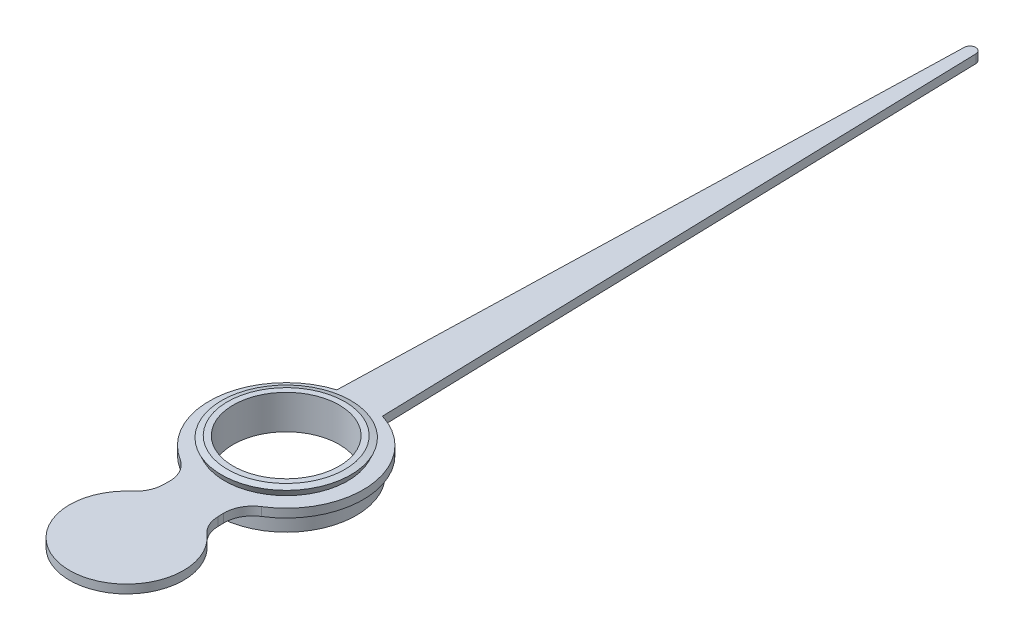
SolidWorks part; units mm, degrees
ref_plane "Face" through (0, 0, 0) normal (0, 0, 1) x (1, 0, 0)
ref_plane "Dessus" through (0, 0, 0) normal (0, 1, 0) x (1, 0, 0)
ref_plane "Droite" through (0, 0, 0) normal (1, 0, 0) x (0, 0, -1)
sketch "Esquisse1" plane through (0, 0, 0) normal (0, 0, 1) x (1, 0, 0)
  line L0 (-1.23, 0) -> (-1.23, 0.3)
  line L1 (-1.23, 0.3) -> (-1.08, 0.3)
  line L2 (-1.08, 0.3) -> (-1.08, 0.45)
  line L3 (-1.0301, 0.6) -> (-0.93, 0.6)
  line L4 (-0.93, 0.6) -> (-0.93, 0)
  line L5 (-0.93, 0) -> (-1.23, 0)
  line L6 (-0.93, 0) -> (0, 0) construction
  line L7 (0, 0) -> (0, 7.0792) construction
  line L8 (-1.08, 0.45) -> (-1.1325, 0.5676)
  line L9 (-1.1325, 0.5676) -> (-1.0301, 0.6)
  dimension "D1" = 1.86
  dimension "D2" = 0.3
  dimension "D3" = 0.3
  dimension "D4" = 0.15
  dimension "D5" = 0.6
  dimension "D6" = 0.0525
  dimension "D7" = 0.1001
  dimension "D8" = 0.15
  dimension "D9" = 0.1176
revolve "Révolution1" add sketch "Esquisse1" angle 360 about L7
sketch "Esquisse2" plane through (0, 0.3, 0) normal (0, 1, 0) x (1, 0, 0)
  line L0 (0.1, 12.0028) -> (0.4, 1.2894)
  line L1 (-0.4804, -1.583) -> (-0.4832, -1.6829)
  line L2 (0, -6.2879) -> (0, -1.265) construction
  line L4 (0.4832, -1.6829) -> (0.4804, -1.583)
  line L5 (0.4, 1.2894) -> (0, 1.2894) construction
  line L6 (0, 1.2894) -> (-0.4, 1.2894) construction
  line L7 (0, 16) -> (0, 1.2894) construction
  line L8 (-0.4, 1.2894) -> (-0.1, 12.0028)
  line L9 (-0.4715, -1.265) -> (0.4715, -1.265) construction
  line L10 (0, -1.08) -> (0, 0) construction
  arc A0 (-0.4, 1.2894) -> (-0.7153, -1.1449) centre (0, 0) ccw
  circle A1 centre (0, 0) radius 1.08
  circle A2 centre (0, 0) radius 1.08 construction
  arc A3 (0.7153, -1.1449) -> (0.4, 1.2894) centre (0, 0) ccw
  arc A4 (-0.6554, -2.0466) -> (0.6554, -2.0466) centre (0, -2.8019) ccw
  arc A5 (0.7153, -1.1449) -> (0.4804, -1.583) centre (0.9802, -1.569) ccw
  arc A6 (0.6554, -2.0466) -> (0.4832, -1.6829) centre (0.983, -1.6689) cw
  arc A7 (-0.6554, -2.0466) -> (-0.4832, -1.6829) centre (-0.983, -1.6689) ccw
  arc A8 (-0.1, 12.0028) -> (0.1, 12.0028) centre (0, 12) cw
  arc A9 (-0.4804, -1.583) -> (-0.7153, -1.1449) centre (-0.9802, -1.569) ccw
  point P26 (0, -3.144)
  dimension "D1" = 2.7
  dimension "D5" = 0.1
  dimension "D6" = 1
  dimension "D7" = 12
  dimension "D8" = 0.1
  dimension "D4" = 0.5
  dimension "D2" = 16
  dimension "D3" = 0.8
extrude "Boss.-Extru.1" add sketch "Esquisse2" along normal blind 0.15
